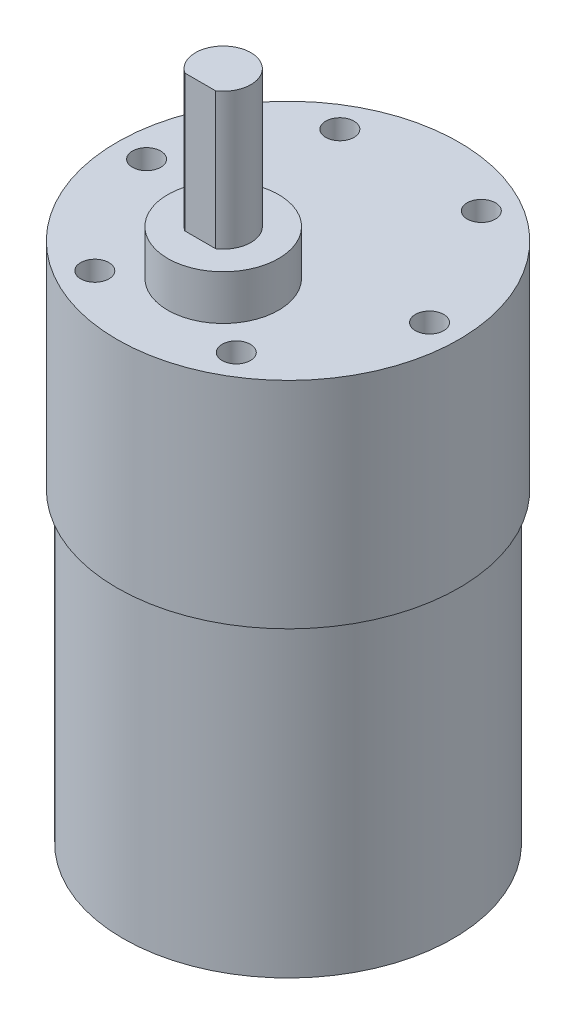
SolidWorks part; units mm, degrees
ref_plane "Front Plane" through (0, 0, 0) normal (0, 0, 1) x (1, 0, 0)
ref_plane "Top Plane" through (0, 0, 0) normal (0, 1, 0) x (1, 0, 0)
ref_plane "Right Plane" through (0, 0, 0) normal (1, 0, 0) x (0, 0, -1)
sketch "Sketch1" plane through (0, 0, 0) normal (0, 1, 0) x (1, 0, 0)
  circle A0 centre (0, 0) radius 17.78
  dimension "D1" = 35.56
extrude "Boss-Extrude1" add sketch "Sketch1" along normal blind 33.02
sketch "Sketch2" plane through (0, 33.02, 0) normal (0, 1, 0) x (1, 0, 0)
  circle A0 centre (0, 0) radius 18.415
  dimension "D1" = 36.83
extrude "Boss-Extrude2" add sketch "Sketch2" along normal blind 23.1775
sketch "Sketch3" plane through (0, 56.1975, 0) normal (0, 1, 0) x (1, 0, 0)
  line L0 (0, 0) -> (23.3389, 0) construction
  line L1 (0, 0) -> (0, 22.8201) construction
  circle A0 centre (15.24, 0) radius 1.524
  circle A1 centre (7.62, -13.1982) radius 1.524
  circle A2 centre (-7.62, -13.1982) radius 1.524
  circle A3 centre (-15.24, 0) radius 1.524
  circle A4 centre (-7.62, 13.1982) radius 1.524
  circle A5 centre (7.62, 13.1982) radius 1.524
  point P19 (0, 0)
  dimension "D2" = 3.048
  dimension "D1" = 15.24
  dimension "D3" = 6
extrude "Cut-Extrude1" cut sketch "Sketch3" against normal blind 12.7
sketch "Sketch4" plane through (0, 56.1975, 0) normal (0, 1, 0) x (1, 0, 0)
  line L0 (0, 0) -> (18.415, 0) construction
  line L1 (0, 0) -> (0, -18.415) construction
  circle A0 centre (0, 0) radius 18.415 construction
  circle A1 centre (0, -6.985) radius 5.969
  dimension "D1" = 11.938
  dimension "D2" = 11.43
extrude "Boss-Extrude3" add sketch "Sketch4" along normal blind 4.826
sketch "Sketch5" plane through (0, 61.0235, 0) normal (0, 1, 0) x (1, 0, 0)
  line L0 (0, -6.985) -> (0, -9.9695) construction
  line L1 (0, -6.985) -> (2.9845, -6.985) construction
  line L2 (0, -9.4615) -> (1.6656, -9.4615) construction
  line L3 (1.6656, -9.4615) -> (-1.6656, -9.4615)
  circle A0 centre (0, -6.985) radius 2.9845 construction
  arc A1 (1.6656, -9.4615) -> (-1.6656, -9.4615) centre (0, -6.985) ccw
  dimension "D1" = 5.969
  dimension "D2" = 0.508
extrude "Boss-Extrude4" add sketch "Sketch5" along normal blind 14.732 contours L3 A1
